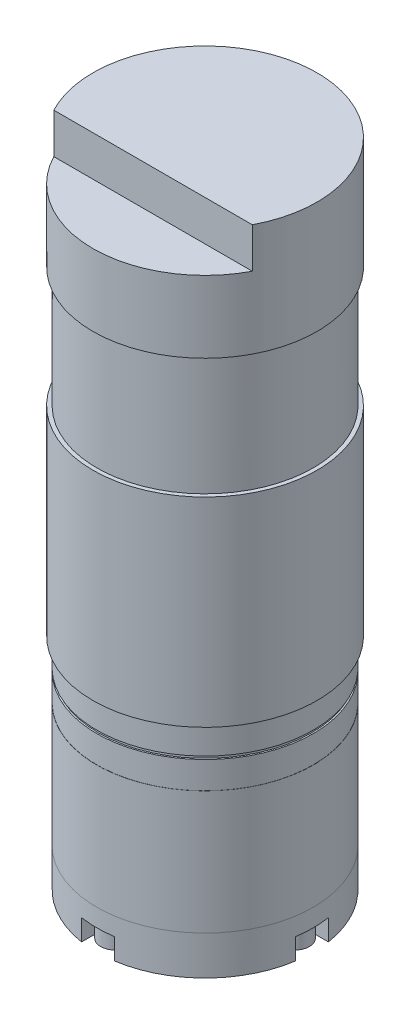
SolidWorks part; units mm, degrees
material "Alloy Steel (SS)"
ref_plane "Front Plane" through (0, 0, 0) normal (0, 0, 1) x (1, 0, 0)
ref_plane "Top Plane" through (0, 0, 0) normal (0, 1, 0) x (1, 0, 0)
ref_plane "Right Plane" through (0, 0, 0) normal (1, 0, 0) x (0, 0, -1)
sketch "Sketch1" plane through (0, 0, 0) normal (0, 1, 0) x (1, 0, 0)
  circle A0 centre (0, 0) radius 18
  dimension "D1" = 36
extrude "Boss-Extrude1" add sketch "Sketch1" along normal blind 89.8
sketch "Sketch2" plane through (0, 89.8, 0) normal (0, 1, 0) x (1, 0, 0)
  circle A0 centre (0, 0) radius 18.65
  dimension "D1" = 37.3
extrude "Boss-Extrude2" add sketch "Sketch2" along normal blind 18.65
ref_plane "Plane1" through (0, 69.8, 0) normal (0, -1, 0) x (-1, 0, 0)
sketch "Sketch9" plane through (0, 0, 0) normal (0, -1, 0) x (1, 0, 0)
  line L1 (4.5826, -10) -> (-4.5826, -10)
  line L2 (4.5826, 10) -> (-4.5826, 10)
  arc A0 (4.5826, -10) -> (4.5826, 10) centre (0, 0) ccw
  arc A1 (-4.5826, 10) -> (-4.5826, -10) centre (0, 0) ccw
  point P6 (0, 0)
  point P9 (0, -10)
  point P12 (0, 10)
  dimension "D1" = 22
  dimension "D2" = 9.1652
  dimension "D3" = 9.1652
extrude "Boss-Extrude4" add sketch "Sketch9" along normal blind 1.3
sketch "Sketch3" plane through (0, 69.8, 0) normal (0, -1, 0) x (-1, 0, 0)
  circle A0 centre (0, 0) radius 18.65
  dimension "D1" = 37.3
extrude "Boss-Extrude3" add sketch "Sketch3" along normal blind 33.2
sketch "Sketch11" plane through (0, -1.3, 0) normal (0, -1, 0) x (1, 0, 0)
  circle A0 centre (0, 0) radius 4
  dimension "D1" = 8
extrude "Cut-Extrude1" cut sketch "Sketch11" against normal blind 10.3
sketch "Sketch13" plane through (0, 108.45, 0) normal (0, 1, 0) x (1, 0, 0)
  line L1 (-16.5227, -8.65) -> (16.5227, -8.65)
  circle A0 centre (0, 0) radius 18.65 construction
  arc A1 (16.5227, -8.65) -> (-16.5227, -8.65) centre (0, 0) cw
  point P9 (0, -8.65)
extrude "Cut-Extrude2" cut sketch "Sketch13" against normal blind 6.7
sketch "Sketch14" plane through (0, 0, 0) normal (0, -1, 0) x (1, 0, 0)
  circle A5 centre (-9.8995, 9.8995) radius 1.5
  circle A6 centre (9.8995, 9.8995) radius 1.5
  circle A7 centre (9.8995, -9.8995) radius 1.5
  circle A8 centre (-9.8995, -9.8995) radius 1.5
  point P8 (0, 0)
  point P15 (0, 0)
  point P17 (0, 0)
  point P20 (0, 0)
  dimension "D2" = 3
  dimension "D3" = 3
  dimension "D4" = 3
  dimension "D5" = 3
extrude "Cut-Extrude3" cut sketch "Sketch14" against normal blind 10
ref_plane "Plane2" through (0, 6.5, 0) normal (0, -1, 0) x (-1, 0, 0)
sketch "Sketch16" plane through (0, 6.5, 0) normal (0, -1, 0) x (-1, 0, 0)
  circle A0 centre (0, 0) radius 18.025
  dimension "D1" = 36.05
extrude "Boss-Extrude5" add sketch "Sketch16" against normal blind 20.5
ref_plane "Plane3" through (0, 31.5, 0) normal (0, -1, 0) x (-1, 0, 0)
sketch "Sketch17" plane through (0, 31.5, 0) normal (0, -1, 0) x (-1, 0, 0)
  circle A0 centre (0, 0) radius 17.75
  circle A1 centre (0, 0) radius 19.6457
extrude "Cut-Extrude5" cut sketch "Sketch17" against normal blind 0.5
sketch "Sketch18" plane through (0, 0, 0) normal (0, -1, 0) x (1, 0, 0)
  line L0 (2.75, -15) -> (2.75, -20)
  line L1 (2.75, -20) -> (-2.75, -20)
  line L2 (-2.75, -20) -> (-2.75, -15)
  line L3 (2.75, 15) -> (2.75, 20)
  line L4 (2.75, 20) -> (-2.75, 20)
  line L5 (-2.75, 20) -> (-2.75, 15)
  line L6 (-15, 2.75) -> (-20, 2.75)
  line L7 (-20, 2.75) -> (-20, -2.75)
  line L8 (-20, -2.75) -> (-15, -2.75)
  line L9 (15, -2.75) -> (20, -2.75)
  line L10 (20, -2.75) -> (20, 2.75)
  line L11 (20, 2.75) -> (15, 2.75)
  circle A0 centre (0, 0) radius 15 construction
  arc A1 (2.75, -15) -> (-2.75, -15) centre (0, -15) ccw
  arc A5 (15, 2.75) -> (15, -2.75) centre (15, 0) ccw
  arc A6 (-2.75, 15) -> (2.75, 15) centre (0, 15) ccw
  arc A7 (-15, -2.75) -> (-15, 2.75) centre (-15, 0) ccw
  point P14 (0, 0)
  dimension "D1" = 30
  dimension "D2" = 5.5
  dimension "D3" = 5.5
  dimension "D4" = 5.5
  dimension "D5" = 5.5
  dimension "D6" = 20
  dimension "D7" = 20
  dimension "D8" = 2.75
  dimension "D9" = 20
  dimension "D10" = 20
  dimension "D11" = 2.75
extrude "Cut-Extrude6" cut sketch "Sketch18" against normal blind 3.5
sketch "Sketch19" plane through (0, 3.5, 0) normal (0, -1, 0) x (1, 0, 0)
  circle A0 centre (-15, 0) radius 2.375
  circle A1 centre (0, 15) radius 2.375
  circle A2 centre (15, 0) radius 2.375
  circle A3 centre (0, -15) radius 2.375
  point P12 (0, 0)
  dimension "D2" = 4.75
  dimension "D1" = 4
extrude "Boss-Extrude6" add sketch "Sketch19" along normal blind 3
sketch "Sketch20" plane through (0, 0.5, 0) normal (0, -1, 0) x (1, 0, 0)
  line L0 (16.5158, 0.8752) -> (15, 1.7503)
  line L1 (-1.7503, 15) -> (-0.8752, 13.4842)
  line L2 (-0.8752, 13.4842) -> (0.8752, 13.4842)
  line L3 (0.8752, 13.4842) -> (1.7503, 15)
  line L4 (1.7503, 15) -> (0.8752, 16.5158)
  line L5 (0.8752, 16.5158) -> (-0.8752, 16.5158)
  line L6 (-0.8752, 16.5158) -> (-1.7503, 15)
  line L7 (16.5158, -0.8752) -> (16.5158, 0.8752)
  line L8 (15, -1.7503) -> (16.5158, -0.8752)
  line L9 (13.4842, -0.8752) -> (15, -1.7503)
  line L10 (13.4842, 0.8752) -> (13.4842, -0.8752)
  line L11 (15, 1.7503) -> (13.4842, 0.8752)
  line L12 (0.8752, -16.5158) -> (1.7503, -15)
  line L13 (-0.8752, -16.5158) -> (0.8752, -16.5158)
  line L14 (-1.7503, -15) -> (-0.8752, -16.5158)
  line L15 (-0.8752, -13.4842) -> (-1.7503, -15)
  line L16 (0.8752, -13.4842) -> (-0.8752, -13.4842)
  line L17 (1.7503, -15) -> (0.8752, -13.4842)
  line L18 (-16.5158, -0.8752) -> (-15, -1.7503)
  line L19 (-16.5158, 0.8752) -> (-16.5158, -0.8752)
  line L20 (-15, 1.7503) -> (-16.5158, 0.8752)
  line L21 (-13.4842, 0.8752) -> (-15, 1.7503)
  line L22 (-13.4842, -0.8752) -> (-13.4842, 0.8752)
  line L23 (-15, -1.7503) -> (-13.4842, -0.8752)
  circle A0 centre (0, 15) radius 1.5158 construction
  point P30 (0, 0)
  dimension "D1" = 4
extrude "Cut-Extrude7" cut sketch "Sketch20" against normal blind 3
sketch "Sketch21" plane through (0, -1.3, 0) normal (0, -1, 0) x (1, 0, 0)
  line L2 (-4.5826, -10) -> (4.5826, -10)
  line L3 (4.5826, 10) -> (-4.5826, 10)
  line L4 (-4.5826, -10) -> (4.5826, -10)
  line L5 (4.5826, 10) -> (-4.5826, 10)
  arc A2 (-4.5826, 10) -> (-4.5826, -10) centre (0, 0) ccw
  arc A3 (4.5826, -10) -> (4.5826, 10) centre (0, 0) ccw
  arc A4 (-4.5826, 10) -> (-4.5826, -10) centre (0, 0) ccw
  arc A5 (4.5826, -10) -> (4.5826, 10) centre (0, 0) ccw
  dimension "D1" = 0
